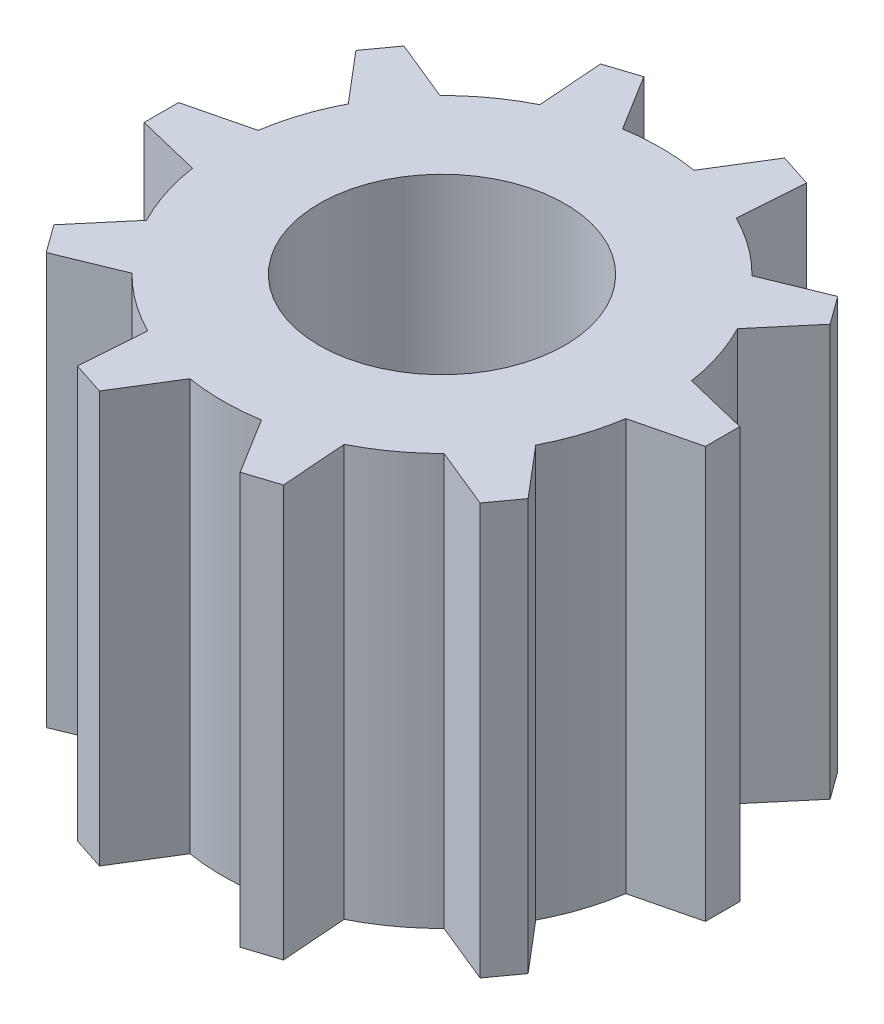
SolidWorks part; units mm, degrees
ref_plane "Front Plane" through (0, 0, 0) normal (0, 0, 1) x (1, 0, 0)
ref_plane "Top Plane" through (0, 0, 0) normal (0, 1, 0) x (1, 0, 0)
ref_plane "Right Plane" through (0, 0, 0) normal (1, 0, 0) x (0, 0, -1)
sketch "Sketch1" plane through (0, 0, 0) normal (0, 1, 0) x (1, 0, 0)
  line L3 (4.57, 0) -> (4.57, -0.28)
  line L4 (4.57, 0) -> (4.57, 0.28)
  line L5 (4.57, -0.28) -> (3.2653, -0.6004)
  line L6 (4.57, 0.28) -> (3.2656, 0.5985)
  circle A0 centre (0, 0) radius 3.57
  arc A1 (3.32, 0) -> (3.1402, 1.0779) centre (0, 0) ccw construction
  arc A2 (3.32, 0) -> (3.1327, -1.0993) centre (0, 0) cw construction
  arc A3 (3.2653, -0.6004) -> (3.2656, 0.5985) centre (0, 0) ccw
  point P3 (3.32, 0)
  point P10 (4.57, 0)
  dimension "D1" = 7.14
  dimension "D2" = 3.32
  dimension "D5" = 4.57
  dimension "D6" = 0.28
  dimension "D7" = 0.28
  dimension "D8" = 1.3435
  dimension "D9" = 1.3427
extrude "Boss-Extrude1" add sketch "Sketch1" along normal blind 6.7 contours A0 L5 L3 L4 L6
pattern_circular "CirPattern1" count 10 over 360 about axis through (0, 0, 0) along (0, 1, 0) of "Boss-Extrude1"
sketch "Sketch2" plane through (0, 6.7, 0) normal (0, 1, 0) x (1, 0, 0)
  circle A0 centre (0, 0) radius 2
  dimension "D1" = 4
extrude "Cut-Extrude1" cut sketch "Sketch2" against normal blind 6.7
